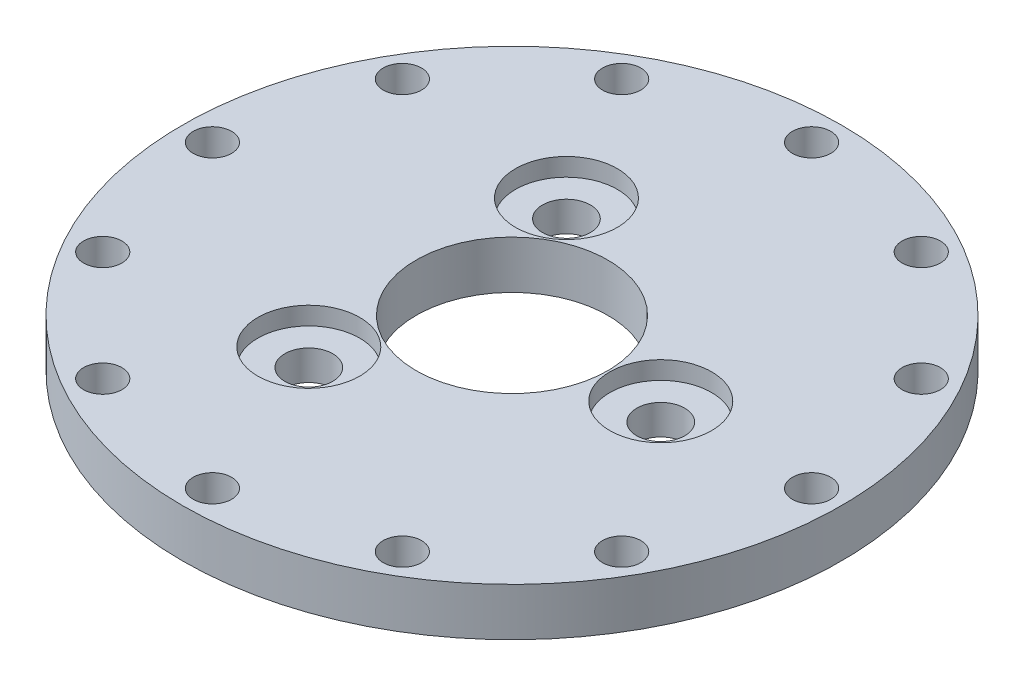
SolidWorks part; units mm, degrees
ref_plane "Front Plane" through (0, 0, 0) normal (0, 0, 1) x (1, 0, 0)
ref_plane "Top Plane" through (0, 0, 0) normal (0, 1, 0) x (1, 0, 0)
ref_plane "Right Plane" through (0, 0, 0) normal (1, 0, 0) x (0, 0, -1)
sketch "Sketch1" plane through (0, 0, 0) normal (0, 1, 0) x (1, 0, 0)
  line L1 (12.413, 0) -> (-6.2065, 10.75) construction
  line L2 (-6.2065, 10.75) -> (-6.2065, -10.75) construction
  line L3 (-6.2065, -10.75) -> (12.413, 0) construction
  circle A0 centre (0, 0) radius 27.5
  circle A1 centre (0, 0) radius 25 construction
  circle A2 centre (0, 25) radius 1.6
  circle A3 centre (12.5, 21.6506) radius 1.6
  circle A4 centre (21.6506, 12.5) radius 1.6
  circle A5 centre (25, 0) radius 1.6
  circle A6 centre (21.6506, -12.5) radius 1.6
  circle A7 centre (12.5, -21.6506) radius 1.6
  circle A8 centre (0, -25) radius 1.6
  circle A9 centre (-12.5, -21.6506) radius 1.6
  circle A10 centre (-21.6506, -12.5) radius 1.6
  circle A11 centre (-25, 0) radius 1.6
  circle A12 centre (-21.6506, 12.5) radius 1.6
  circle A13 centre (-12.5, 21.6506) radius 1.6
  circle A14 centre (0, 0) radius 8
  circle A15 centre (0, 0) radius 6.2065 construction
  circle A16 centre (12.413, 0) radius 2
  circle A17 centre (-6.2065, -10.75) radius 2
  circle A18 centre (-6.2065, 10.75) radius 2
  point P31 (0, 0)
  point P42 (0, 0)
  dimension "D1" = 55
  dimension "D2" = 50
  dimension "D3" = 3.2
  dimension "D5" = 16
  dimension "D7" = 4
  dimension "D6" = 21.5
  dimension "D4" = 12
  dimension "D8" = 3
extrude "Boss-Extrude1" add sketch "Sketch1" along normal blind 4
sketch "Sketch2" plane through (0, 4, 0) normal (0, 1, 0) x (1, 0, 0)
  circle A0 centre (-6.2065, 10.75) radius 4.25
  circle A1 centre (12.413, 0) radius 4.25
  circle A2 centre (-6.2065, -10.75) radius 4.25
  point P9 (0, 0)
  dimension "D1" = 8.5
  dimension "D2" = 3
extrude "Cut-Extrude1" cut sketch "Sketch2" against normal blind 1.5
